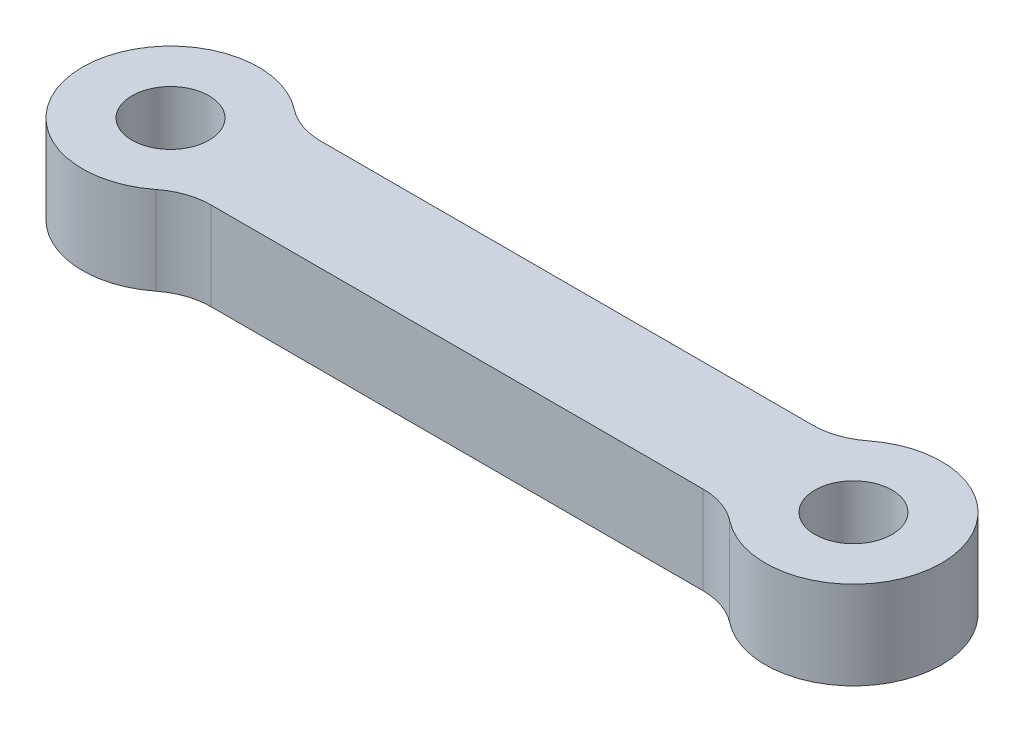
SolidWorks part; units mm, degrees
ref_plane "Front Plane" through (0, 0, 0) normal (0, 0, 1) x (1, 0, 0)
ref_plane "Top Plane" through (0, 0, 0) normal (0, 1, 0) x (1, 0, 0)
ref_plane "Right Plane" through (0, 0, 0) normal (1, 0, 0) x (0, 0, -1)
sketch "Sketch1" plane through (0, 0, 0) normal (0, 1, 0) x (1, 0, 0)
  line L0 (0, 0) -> (31, 0) construction
  line L1 (3.1225, 2.5) -> (27.8775, 2.5)
  line L2 (3.1225, -2.5) -> (27.8775, -2.5)
  circle A0 centre (0, 0) radius 4
  circle A1 centre (31, 0) radius 4
  circle A2 centre (0, 0) radius 1.75
  circle A3 centre (31, 0) radius 1.75
  dimension "D1" = 8
  dimension "D3" = 8
  dimension "D5" = 3.5
  dimension "D6" = 3.5
  dimension "D2" = 31
  dimension "D4" = 2.5
extrude "Boss-Extrude1" add sketch "Sketch1" along normal blind 4
fillet "Fillet1" radius 3 4 edges at (3.1225, 2, 2.5) (27.8775, 2, 2.5) (27.8775, 2, -2.5) (3.1225, 2, -2.5)
